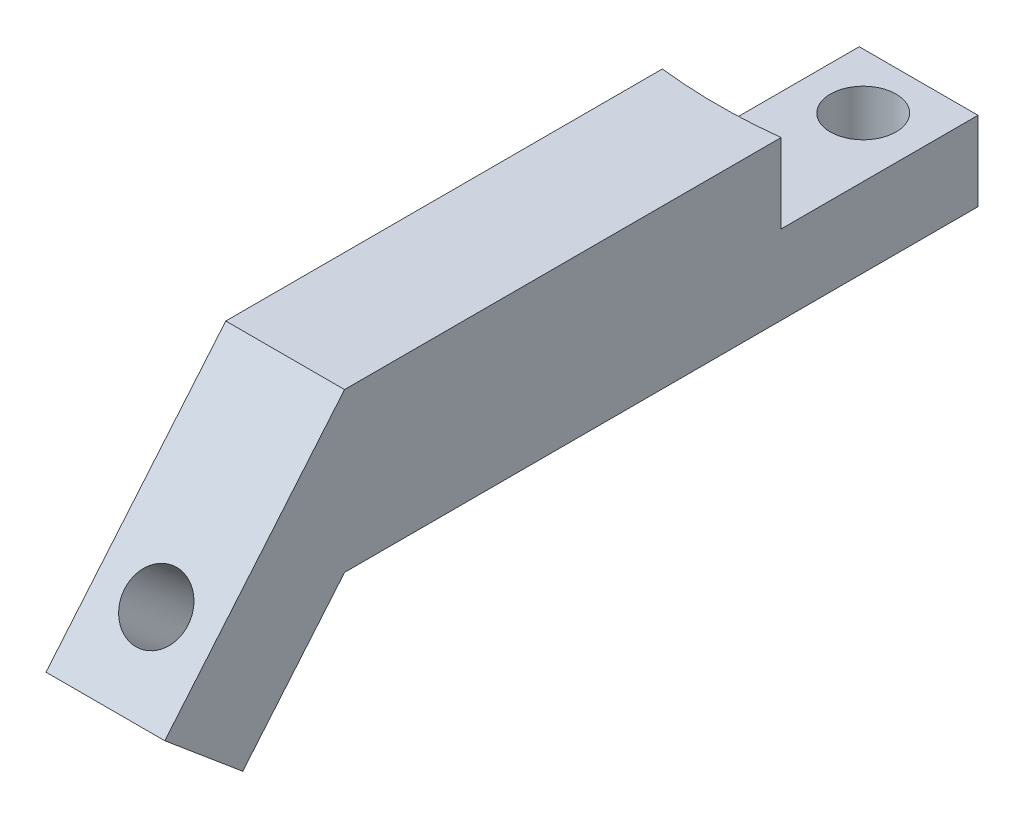
SolidWorks part; units mm, degrees
ref_plane "Спереди" through (0, 0, 0) normal (0, 0, 1) x (1, 0, 0)
ref_plane "Сверху" through (0, 0, 0) normal (0, 1, 0) x (1, 0, 0)
ref_plane "Справа" through (0, 0, 0) normal (1, 0, 0) x (0, 0, -1)
sketch "Sketch1" plane through (0, 0, 0) normal (0, 1, 0) x (1, 0, 0)
  line L0 (0, 40) -> (0, -40) construction
  line L1 (7.5, -40) -> (-7.5, -40)
  line L2 (7.5, -40) -> (7.5, 40)
  line L3 (7.5, 40) -> (-7.5, 40)
  line L4 (-7.5, -40) -> (-7.5, 40)
  line L5 (7.5, -40) -> (-7.5, 40) construction
  line L6 (7.5, 40) -> (-7.5, -40) construction
  circle A0 centre (0, 33) radius 4.15
  circle A1 centre (0, -36) radius 1.5 construction
  point P0 (0, 0)
  dimension "D1" = 8.3
  dimension "D5" = 3
  dimension "D2" = 7
  dimension "D3" = 80
  dimension "D4" = 15
  dimension "D6" = 4
extrude "Boss-Extrude1" add sketch "Sketch1" along normal blind 10
sketch "Sketch2" plane through (0, 10, 0) normal (0, 1, 0) x (1, 0, 0)
  line L0 (0, -40) -> (0, 40) construction
  line L1 (-7.5, -40) -> (7.5, -40) construction
  line L2 (7.5, 40) -> (-7.5, 40) construction
  line L3 (7.5, -40) -> (7.5, 40) construction
  line L4 (-7.5, 40) -> (-7.5, -40) construction
  line L5 (-7.5, 11.1341) -> (-7.5, 15.1341) construction
  line L6 (7.5, 15.1341) -> (7.5, 11.1341) construction
  line L7 (7.5, 15.1341) -> (7.5, -40)
  line L8 (7.5, -40) -> (-7.5, -40)
  line L9 (-7.5, -40) -> (-7.5, 15.1341)
  arc A0 (7.5, 15.1341) -> (-7.5, 15.1341) centre (0, 79.7) cw
  arc A1 (-7.5, 11.1341) -> (7.5, 11.1341) centre (0, 75.7) ccw construction
  point P16 (0, 14.7)
  dimension "D2" = 65
  dimension "D3" = 25.3
  dimension "D1" = 4
extrude "Boss-Extrude2" add sketch "Sketch2" along normal blind 10
sketch "Sketch10" plane through (7.5, 0, 0) normal (1, 0, 0) x (0, 0, -1)
  line L0 (-40, 0) -> (-52.8558, -15.3209)
  line L1 (-52.8558, -15.3209) -> (-62.7038, -7.0574)
  line L2 (-62.7038, -7.0574) -> (-40, 20)
  line L3 (-40, 0) -> (40, 0) construction
  line L6 (-40, 0) -> (-40, 20)
  dimension "D1" = 130
  dimension "D2" = 20
extrude "Boss-Extrude4" add sketch "Sketch10" against normal up to surface (15 mm away) up to face at (-7.5, 10, -5.0447)
sketch "Sketch11" plane through (0, 19.6962, 23.473) normal (0, -0.6428, -0.766) x (-1, 0, 0)
  line L0 (0, -45.7115) -> (0, -25.7115) construction
  line L1 (7.5, -45.7115) -> (-7.5, -45.7115) construction
  line L2 (7.5, -25.7115) -> (-7.5, -25.7115) construction
  circle A0 centre (0, -35.7115) radius 4
  dimension "D1" = 8
extrude "Cut-Extrude5" cut sketch "Sketch11" against normal through all
